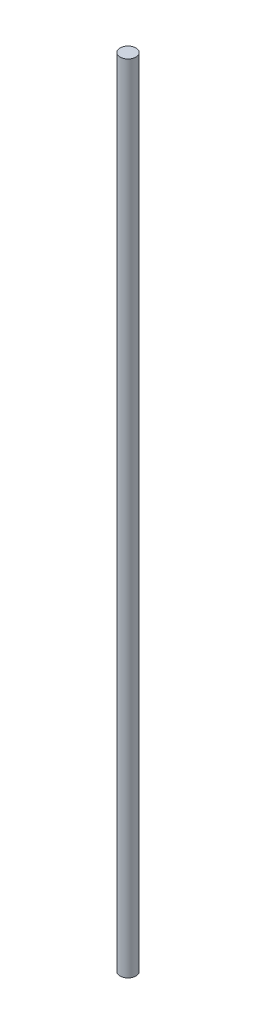
SolidWorks part; units mm, degrees
material "Plain Carbon Steel"
ref_plane "Front Plane" through (0, 0, 0) normal (0, 0, 1) x (1, 0, 0)
ref_plane "Top Plane" through (0, 0, 0) normal (0, 1, 0) x (1, 0, 0)
ref_plane "Right Plane" through (0, 0, 0) normal (1, 0, 0) x (0, 0, -1)
sketch "Sketch1" plane through (0, 0, 0) normal (0, 1, 0) x (1, 0, 0)
  circle A0 centre (0, 0) radius 4
  dimension "D1" = 8
extrude "Boss-Extrude1" add sketch "Sketch1" along normal blind 400
equation "\"Diameter\"= 8mm"
equation "\"Length\"= 400mm"
equation "\"D1@Sketch1\"=\"Diameter\""
equation "\"D1@Boss-Extrude1\"=\"Length\""
